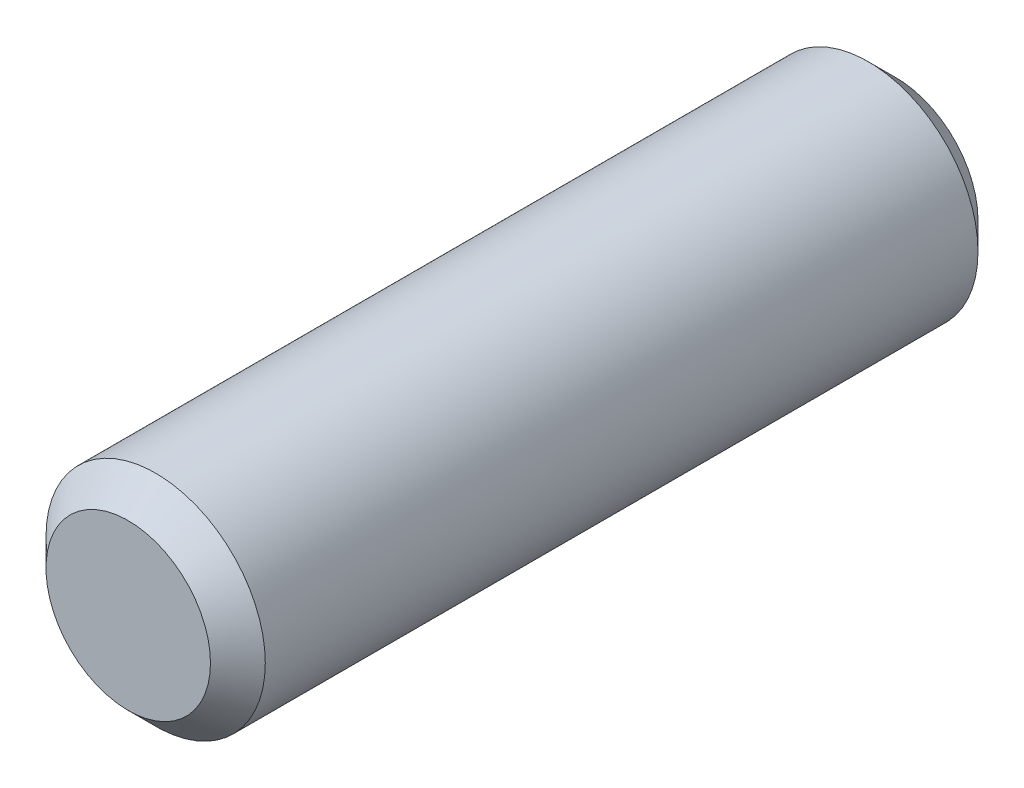
SolidWorks part; units mm, degrees
ref_plane "Front Plane" through (0, 0, 0) normal (0, 0, 1) x (1, 0, 0)
ref_plane "Top Plane" through (0, 0, 0) normal (0, 1, 0) x (1, 0, 0)
ref_plane "Right Plane" through (0, 0, 0) normal (1, 0, 0) x (0, 0, -1)
sketch "Sketch1" plane through (0, 0, 0) normal (0, 0, 1) x (1, 0, 0)
  circle A0 centre (0, 0) radius 2
  dimension "D1" = 4
extrude "Boss-Extrude1" add sketch "Sketch1" along normal blind 14
chamfer "Chamfer1" distance 0.5 angle 45 2 edges at (2, 0, 0) (2, 0, 14)
